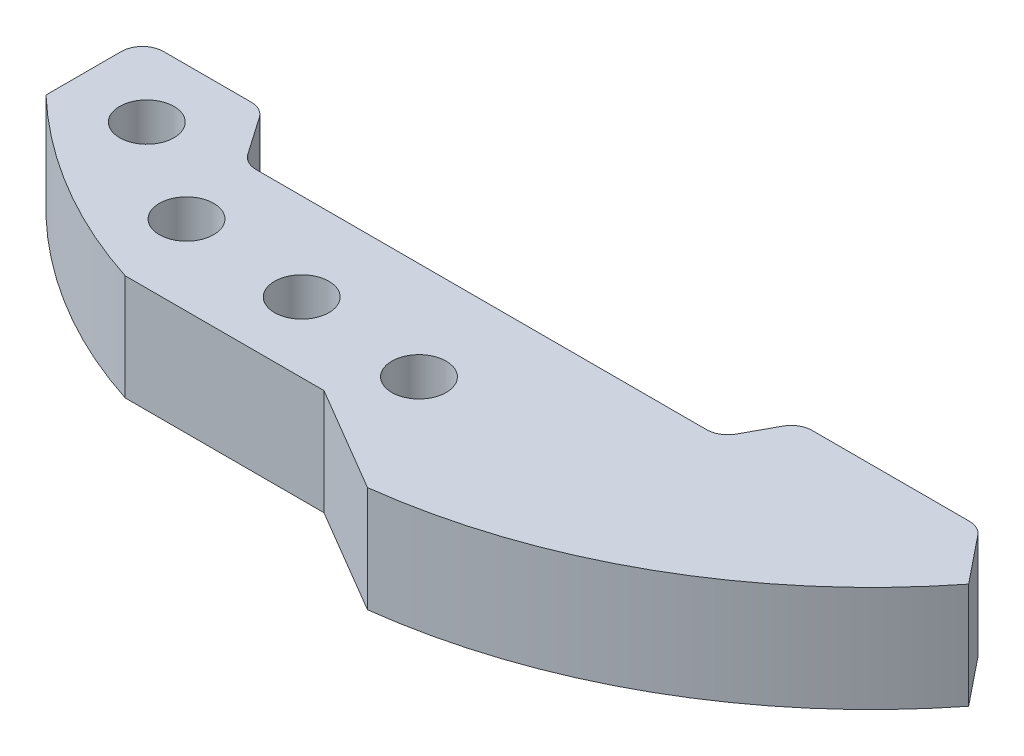
SolidWorks part; units mm, degrees
material "PE High Density"
ref_plane "Front Plane" through (0, 0, 0) normal (0, 0, 1) x (1, 0, 0)
ref_plane "Top Plane" through (0, 0, 0) normal (0, 1, 0) x (1, 0, 0)
ref_plane "Right Plane" through (0, 0, 0) normal (1, 0, 0) x (0, 0, -1)
sketch "Sketch1" plane through (0, 0, 0) normal (0, 1, 0) x (1, 0, 0)
  line L0 (-8.8733, 0) -> (45.2043, 0)
  line L1 (76.9724, -0.3288) -> (72.6275, 5.0746) construction
  line L2 (49.3913, 4.9266) -> (47.4362, 1.3275)
  line L3 (51.6233, 6.2542) -> (70.4621, 6.2542)
  line L4 (72.4415, 5.3058) -> (76.9724, -0.3288)
  line L5 (29.5955, 0) -> (-8.8733, 0) construction
  line L6 (49.3913, 4.9266) -> (48.9611, 4.1345) construction
  line L7 (30.8655, -26.3694) -> (18.1655, -18.896)
  line L8 (18.1655, -18.896) -> (-5.6888, -18.896)
  line L9 (-29.2338, -4.8553) -> (-29.2338, 4.1773)
  line L10 (-26.6938, 6.7173) -> (-16.1913, 6.7173)
  line L11 (-14.1042, 5.6249) -> (-10.9603, 1.0924)
  arc A0 (-8.8733, 0) -> (-10.9603, 1.0924) centre (-8.8733, 2.54) cw
  arc A1 (45.2043, 0) -> (47.4362, 1.3275) centre (45.2043, 2.54) ccw
  arc A2 (45.2043, 0) -> (47.4362, 1.3275) centre (45.2043, 2.54) ccw construction
  circle A3 centre (-20.3688, -1.6242) radius 3.2639
  circle A4 centre (-7.9084, -9.3171) radius 3.2639
  circle A5 centre (7.107, -10.5038) radius 3.2639
  arc A6 (-10.9603, 1.0924) -> (-8.8733, 0) centre (-8.8733, 2.54) ccw construction
  arc A7 (-16.1913, 6.7173) -> (-14.1042, 5.6249) centre (-16.1913, 4.1773) cw
  arc A8 (-26.6938, 6.7173) -> (-29.2338, 4.1773) centre (-26.6938, 4.1773) ccw
  arc A9 (-29.2338, -4.8553) -> (-5.6888, -18.896) centre (13.2373, 39.6028) ccw
  arc A10 (30.8655, -26.3694) -> (76.9724, -0.3288) centre (22.2088, 42.7962) ccw
  arc A11 (30.8655, -26.3694) -> (76.9724, -0.3288) centre (22.2088, 42.7962) ccw construction
  arc A12 (70.4621, 6.2542) -> (72.4415, 5.3058) centre (70.4621, 3.7142) cw
  circle A13 centre (22.4448, -11.7675) radius 3.2639
  arc A14 (72.4415, 5.3058) -> (70.4621, 6.2542) centre (70.4621, 3.7142) ccw construction
  arc A15 (51.6233, 6.2542) -> (49.3913, 4.9266) centre (51.6233, 3.7142) ccw
  dimension "D1" = 6.5278
extrude "Boss-Extrude1" add sketch "Sketch1" along normal blind 12.7
sketch "Sketch2" [suppressed] plane through (0, 0, 0) normal (0, -1, 0) x (1, 0, 0)
  line L1 (-14.3901, -1.0096) -> (-15.0985, 5.485)
  line L2 (-15.0985, 5.485) -> (-21.0772, 8.1188)
  line L3 (-21.0772, 8.1188) -> (-26.3475, 4.258)
  line L4 (-26.3475, 4.258) -> (-25.6391, -2.2366)
  line L5 (-25.6391, -2.2366) -> (-19.6604, -4.8704)
  line L6 (-19.6604, -4.8704) -> (-14.3901, -1.0096)
  line L13 (13.6393, 10.4014) -> (10.4618, 16.1098)
  line L14 (10.4618, 16.1098) -> (3.9295, 16.2122)
  line L15 (3.9295, 16.2122) -> (0.5747, 10.6062)
  line L16 (0.5747, 10.6062) -> (3.7522, 4.8979)
  line L17 (3.7522, 4.8979) -> (10.2845, 4.7955)
  line L18 (10.2845, 4.7955) -> (13.6393, 10.4014)
  circle A0 centre (-20.3688, 1.6242) radius 5.6579 construction
  circle A2 centre (7.107, 10.5038) radius 5.6578 construction
  dimension "D1" = 11.3157
extrude "Cut-Extrude1" [suppressed] cut sketch "Sketch2" against normal through all
chamfer "Chamfer1" [suppressed] distance 4.0894 angle 41
